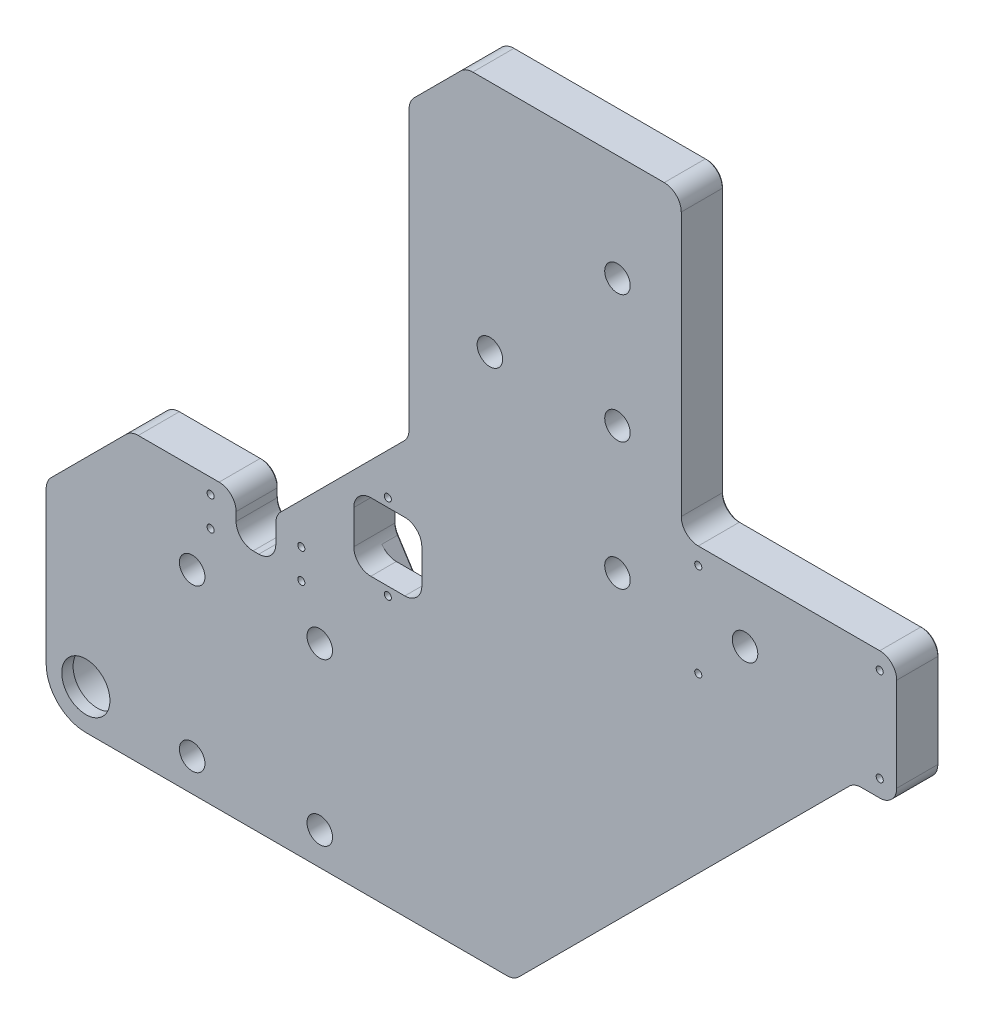
SolidWorks part; units mm, degrees
material "Alumina"
ref_plane "Plan de face" through (0, 0, 0) normal (0, 0, 1) x (1, 0, 0)
ref_plane "Plan de dessus" through (0, 0, 0) normal (0, 1, 0) x (1, 0, 0)
ref_plane "Plan de droite" through (0, 0, 0) normal (1, 0, 0) x (0, 0, -1)
sketch "Esquisse1" plane through (0, 0, 0) normal (0, 0, 1) x (1, 0, 0)
  line L0 (-21.0727, 123.2426) -> (54.9273, 123.2426)
  line L1 (54.9273, 123.2426) -> (54.9273, 18.2426)
  line L2 (54.9273, 18.2426) -> (130.9273, 18.2426)
  line L3 (130.9273, 18.2426) -> (130.9273, -26.7574)
  line L4 (-4.0727, -146.7574) -> (115.9273, -26.7574)
  line L5 (115.9273, -26.7574) -> (130.9273, -26.7574)
  line L6 (-4.0727, -146.7574) -> (-169.0727, -146.7574)
  line L7 (-169.0727, -146.7574) -> (-169.0727, -76.7574)
  line L8 (-21.0727, 123.2426) -> (-41.0727, 103.2426)
  line L11 (-41.0727, 0.2426) -> (-88.0727, -46.7574)
  line L13 (-169.0727, -76.7574) -> (-139.0727, -46.7574)
  line L14 (-41.0727, 103.2426) -> (-41.0727, 0.2426)
  line L16 (-88.0727, -46.7574) -> (-139.0727, -46.7574)
  circle A0 centre (-86.0562, -91.7574) radius 5.5 construction
  point P9 (-41.0727, 123.2426)
  point P15 (-41.0727, -46.7574)
  point P20 (-169.0727, -46.7574)
  dimension "D5" = 55
  dimension "D3" = 76
  dimension "D4" = 45
  dimension "D6" = 105
  dimension "D7" = 45
  dimension "D8" = 100
  dimension "D9" = 128
  dimension "D13" = 165
  dimension "D14" = 120
extrude "Boss.-Extru.1" add sketch "Esquisse1" along normal blind 15
hole_wizard "Chambrage pour vis à tête hexagonale M81" positions "Esquisse2" profile "Esquisse3" counterbore size "M8" standard "ISO" end condition through all
sketch "Esquisse2" plane through (0, 0, 0) normal (0, 0, -1) x (-1, 0, 0)
  line L2 (169.0727, -146.7574) -> (4.0727, -146.7574) construction
  line L3 (169.0727, -76.7574) -> (169.0727, -146.7574) construction
  line L18 (-54.9273, 18.2426) -> (-54.9273, 123.2426) construction
  line L19 (-54.9273, 123.2426) -> (21.0727, 123.2426) construction
  point P0 (72.5727, -78.2574)
  point P3 (117.5727, -78.2574)
  point P6 (72.5727, -135.2574)
  point P9 (117.5727, -135.2574)
  point P101 (-32.4273, 85.7426)
  point P103 (-32.4273, 40.7426)
  point P105 (-32.4273, -4.2574)
  point P107 (-77.4273, -4.2574)
  point P118 (12.5727, 40.7426)
  dimension "D1" = 57
  dimension "D2" = 45
  dimension "D3" = 11.5
  dimension "D4" = 51.5
  dimension "D5" = 22.5
  dimension "D6" = 45
  dimension "D7" = 45
  dimension "D8" = 45
  dimension "D9" = 37.5
  dimension "D10" = 45
sketch "Esquisse3" plane through (-72.5727, -78.2574, 0) normal (1, 0, 0) x (0, 1, 0)
  line L0 (0, 0) -> (0, 15)
  line L1 (0, 15) -> (4.5, 15)
  line L3 (4.5, 15) -> (4.5, 8.6)
  line L4 (4.5, 8.6) -> (7.5, 8.6)
  line L5 (7.5, 8.6) -> (7.5, 0)
  line L7 (7.5, 0) -> (0, 0)
  line L11 (0, -6.35) -> (0, 107.95) construction
  dimension "Diamètre du perçage jusqu'au prochain" = 9
  dimension "Profondeur du perçage jusqu'au prochain" = 15
  dimension "Diamètre du chambrage" = 15
  dimension "Profondeur du chambrage" = 8.6
hole_wizard "Tap Drill for M5 Tap1" positions "Sketch9" profile "Sketch10" hole size "M5" standard "ISO"
sketch "Sketch9" plane through (0, -146.7574, 0) normal (0, -1, 0) x (-1, 0, 0)
  line L0 (169.0727, 0) -> (4.0727, 0) construction
  line L3 (4.0727, -15) -> (4.0727, 0) construction
  point P0 (13.0727, -7.5)
  dimension "D1" = 7.5
  dimension "D2" = 9
sketch "Sketch10" plane through (-13.0727, -146.7574, 7.5) normal (1, 0, 0) x (0, 0, -1)
  line L0 (0, 0) -> (0, 14.2618)
  line L1 (0, 14.2618) -> (2.1, 13)
  line L2 (2.1, 13) -> (2.1, 0)
  line L5 (2.1, 0) -> (0, 0)
  line L10 (0, 14.2618) -> (-2.1, 13) construction
  line L11 (0, -6.35) -> (0, 107.95) construction
  dimension "Hole Dia." = 4.2
  dimension "Hole Depth" = 13
  dimension "Drill Angle" = 118
sketch "Sketch25" plane through (0, 0, 0) normal (0, 0, -1) x (-1, 0, 0)
  line L1 (88.0727, -46.7574) -> (102.0727, -46.7574)
  line L2 (88.0727, -46.7574) -> (88.0727, -61.7574)
  line L3 (88.0727, -61.7574) -> (102.0727, -61.7574)
  line L4 (102.0727, -46.7574) -> (102.0727, -61.7574)
  dimension "D1" = 14
  dimension "D2" = 15
extrude "Cut-Extrude6" cut sketch "Sketch25" against normal through all
fillet "Congé1" radius 6 15 edges at (54.9273, 18.2426, 7.5) (-41.0727, 103.2426, 7.5) (-41.0727, 0.2426, 7.5) (-169.0727, -76.7574, 7.5) (-139.0727, -46.7574, 7.5) (-21.0727, 123.2426, 7.5) (54.9273, 123.2426, 7.5) (130.9273, 18.2426, 7.5) (-4.0727, -146.7574, 7.5) (130.9273, -26.7574, 7.5) (115.9273, -26.7574, 7.5) (-102.0727, -61.7574, 7.5) (-88.0727, -61.7574, 7.5) (-102.0727, -46.7574, 7.5) (-88.0727, -46.7574, 7.5)
sketch "Sketch11" plane through (0, 0, 0) normal (0, 0, -1) x (-1, 0, 0)
  line L0 (169.0727, -79.2427) -> (169.0727, -146.7574) construction
  line L1 (169.0727, -146.7574) -> (6.558, -146.7574) construction
  circle A0 centre (155.0727, -132.7574) radius 8.5
  dimension "D1" = 17
  dimension "D2" = 14
  dimension "D3" = 14
extrude "Cut-Extrude1" cut sketch "Sketch11" against normal through all
sketch "Sketch12" plane through (0, 0, 0) normal (0, 0, -1) x (-1, 0, 0)
  circle A0 centre (155.0727, -132.7574) radius 11
  dimension "D1" = 22
extrude "Cut-Extrude2" cut sketch "Sketch12" against normal blind 11
sketch "Sketch13" plane through (0, 0, 0) normal (0, 0, -1) x (-1, 0, 0)
  line L1 (60.5727, -24.7574) -> (36.5727, -24.7574)
  line L2 (60.5727, -24.7574) -> (60.5727, -48.7574)
  line L3 (60.5727, -48.7574) -> (36.5727, -48.7574)
  line L4 (36.5727, -24.7574) -> (36.5727, -48.7574)
  line L5 (60.5727, -24.7574) -> (36.5727, -48.7574) construction
  line L6 (60.5727, -48.7574) -> (36.5727, -24.7574) construction
  line L8 (108.0727, -46.7574) -> (136.5874, -46.7574) construction
  line L9 (41.0727, 100.7573) -> (41.0727, 2.7279) construction
  point P0 (48.5727, -36.7574)
  dimension "D1" = 10
  dimension "D2" = 7.5
  dimension "D3" = 24
  dimension "D4" = 24
extrude "Cut-Extrude3" cut sketch "Sketch13" against normal through all
fillet "Fillet1" radius 6 4 edges at (-60.5727, -48.7574, 7.5) (-36.5727, -48.7574, 7.5) (-36.5727, -24.7574, 7.5) (-60.5727, -24.7574, 7.5)
sketch "Sketch14" plane through (0, 0, 0) normal (0, 0, -1) x (-1, 0, 0)
  line L11 (48.5727, -36.7574) -> (57.1396, -36.7574) construction
  line L14 (48.5727, -21.7574) -> (48.5727, -51.7574) construction
  line L15 (53.7941, -18.4142) -> (59.6257, -27.5221)
  line L16 (43.3513, -18.4142) -> (37.5197, -27.5221)
  line L17 (36.5727, -30.7574) -> (36.5727, -42.7574)
  line L18 (60.5727, -42.7574) -> (60.5727, -30.7574)
  line L20 (43.3513, -55.1006) -> (37.5197, -45.9927)
  line L21 (53.7941, -55.1006) -> (59.6257, -45.9927)
  arc A10 (53.7941, -18.4142) -> (43.3513, -18.4142) centre (48.5727, -21.7574) ccw
  arc A11 (43.3513, -55.1006) -> (53.7941, -55.1006) centre (48.5727, -51.7574) ccw
  arc A12 (36.5727, -42.7574) -> (37.5197, -45.9927) centre (42.5727, -42.7574) ccw
  arc A13 (59.6257, -45.9927) -> (60.5727, -42.7574) centre (54.5727, -42.7574) ccw
  arc A14 (37.5197, -27.5221) -> (36.5727, -30.7574) centre (42.5727, -30.7574) ccw
  arc A15 (60.5727, -30.7574) -> (59.6257, -27.5221) centre (54.5727, -30.7574) ccw
  point P5 (48.5727, -36.7574)
  dimension "D4" = 6.2
extrude "Cut-Extrude4" cut sketch "Sketch14" against normal blind 6
fillet "Fillet3" radius 14 1 edges at (-169.0727, -146.7574, 7.5)
hole_wizard "Tap Drill for M3 Tap1" positions "Sketch15" profile "Sketch16" hole size "M3" standard "ISO" end condition through all
sketch "Sketch15" plane through (0, 0, 6) normal (0, 0, -1) x (-1, 0, 0)
  point P1 (48.5727, -21.7574)
  point P4 (48.5727, -51.7574)
sketch "Sketch16" plane through (-48.5727, -21.7574, 6) normal (1, 0, 0) x (0, 1, 0)
  line L0 (0, 0) -> (0, 9)
  line L1 (0, 9) -> (1.25, 9)
  line L2 (1.25, 9) -> (1.25, 0)
  line L5 (1.25, 0) -> (0, 0)
  line L11 (0, -6.35) -> (0, 107.95) construction
  dimension "Thru Hole Dia." = 2.5
  dimension "Thru Hole Depth" = 9
chamfer "Chamfer1" distance 0.5 angle 45 54 edges at (-166.0727, -132.7574, 0) (-125.0727, -135.2574, 0) (-80.0727, -135.2574, 0) (-125.0727, -78.2574, 0) (-80.0727, -78.2574, 0) (-20.0727, 40.7426, 0) (69.9273, -4.2574, 0) (24.9273, 85.7426, 0) (24.9273, 40.7426, 0) (24.9273, -4.2574, 0) (130.9273, -4.2574, 0) (-80.8153, -146.7574, 0) (129.17, 16.4852, 0) (92.9273, 18.2426, 0) (-169.0727, -106, 0) (56.6847, 20, 0) (-168.616, -76.9466, 0) (54.9273, 70.7426, 0) (-154.0727, -61.7574, 0) (53.17, 121.4852, 0) (-138.8835, -47.2141, 0) (15.17, 123.2426, 0) (-122.33, -46.7574, 0) (-20.8835, 122.7859, 0) (-31.0727, 113.2426, 0) (-64.5727, -23.2574, 0) (-40.616, 103.0534, 0) (-41.5294, 0.4318, 0) (-41.0727, 51.7426, 0) (-36.8143, -44.4429, 0) (-36.5727, -36.7574, 0) (-36.8143, -29.0719, 0) (-60.3311, -44.4429, 0) (-60.5727, -36.7574, 0) (-60.3311, -29.0719, 0) (116.1165, -27.2141, 0) (121.67, -26.7574, 0) (55.9273, -86.7574, 0) (129.17, -25, 0) (-4.2619, -146.3007, 0) (-164.9722, -142.6569, 0) (-40.4355, -50.5467, 0) (-48.5727, -57.9574, 0) (-40.4355, -22.9682, 0) (-56.7099, -50.5467, 0) (-48.5727, -15.5574, 0) (-56.7099, -22.9682, 0) (-103.83, -48.5148, 0) (-102.0727, -54.2574, 0) (-100.3153, -60, 0) (-95.0727, -61.7574, 0) (-89.83, -60, 0) (-88.0727, -52.5, 0) (-87.616, -46.9466, 0)
hole_wizard "Tap Drill for M3 Tap2" positions "Sketch18" profile "Sketch19" hole size "M3" standard "ISO" end condition through all
sketch "Sketch18" plane through (0, 0, 0) normal (0, 0, -1) x (-1, 0, 0)
  point P0 (-124.9273, 12.2426)
  point P3 (-124.9273, -20.7574)
  point P6 (-60.9273, 12.2426)
  point P8 (-60.9273, -20.7574)
sketch "Sketch19" plane through (124.9273, 12.2426, 0) normal (1, 0, 0) x (0, 1, 0)
  line L0 (0, 0) -> (0, 15)
  line L1 (0, 15) -> (1.25, 15)
  line L2 (1.25, 15) -> (1.25, 0)
  line L5 (1.25, 0) -> (0, 0)
  line L11 (0, -6.35) -> (0, 107.95) construction
  dimension "Thru Hole Dia." = 2.5
  dimension "Thru Hole Depth" = 15
hole_wizard "Tap Drill for M3 Tap3" positions "Sketch22" profile "Sketch23" hole size "M3" standard "ISO" end condition through all
sketch "Sketch22" plane through (0, 0, 15) normal (0, 0, 1) x (1, 0, 0)
  line L1 (-108.0727, -46.7574) -> (-136.5874, -46.7574) construction
  circle A1 centre (-117.5727, -78.2574) radius 4.5 construction
  point P0 (-111.0727, -52.0574)
  point P2 (-111.0727, -62.4574)
  point P4 (-79.0727, -62.4574)
  point P6 (-79.0727, -52.0574)
  dimension "D3" = 6.5
  dimension "D1" = 32
  dimension "D2" = 10.4
  dimension "D4" = 5.3
sketch "Sketch23" plane through (-111.0727, -52.0574, 15) normal (1, 0, 0) x (0, -1, 0)
  line L0 (0, 0) -> (0, 15)
  line L1 (0, 15) -> (1.25, 15)
  line L2 (1.25, 15) -> (1.25, 0)
  line L5 (1.25, 0) -> (0, 0)
  line L11 (0, -6.35) -> (0, 107.95) construction
  dimension "Thru Hole Dia." = 2.5
  dimension "Thru Hole Depth" = 15
hole_wizard "Trou pour taraudage pour trou taraudé M61" positions "Esquisse4" profile "Esquisse5" hole size "M6" standard "ISO"
sketch "Esquisse4" plane through (0, -146.7574, 0) normal (0, -1, 0) x (-1, 0, 0)
  line L0 (6.558, 0) -> (155.0727, 0) construction
  point P0 (35.6158, -7.5)
  point P3 (85.6158, -7.5)
  dimension "D1" = 50
  dimension "D2" = 7.5
sketch "Esquisse5" plane through (-35.6158, -146.7574, 7.5) normal (1, 0, 0) x (0, 0, -1)
  line L0 (0, 0) -> (0, 21.5022)
  line L1 (0, 21.5022) -> (2.5, 20)
  line L2 (2.5, 20) -> (2.5, 0)
  line L5 (2.5, 0) -> (0, 0)
  line L10 (0, 21.5022) -> (-2.5, 20) construction
  line L11 (0, -6.35) -> (0, 107.95) construction
  dimension "Diamètre du perçage" = 5
  dimension "Profondeur du perçage" = 20
  dimension "Angle de pointe" = 118
